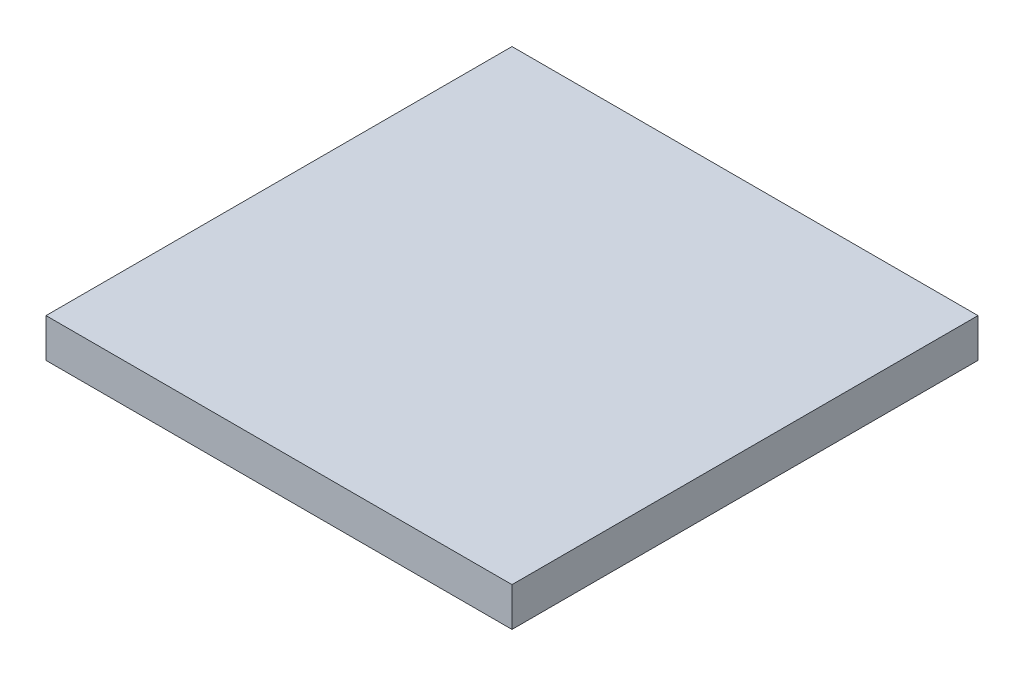
SolidWorks part; units mm, degrees
ref_plane "Front Plane" through (0, 0, 0) normal (0, 0, 1) x (1, 0, 0)
ref_plane "Top Plane" through (0, 0, 0) normal (0, 1, 0) x (1, 0, 0)
ref_plane "Right Plane" through (0, 0, 0) normal (1, 0, 0) x (0, 0, -1)
sketch "BaseS" plane through (0, 0, 0) normal (0, 1, 0) x (1, 0, 0)
  line L1 (-0.6, 0.6) -> (0.6, 0.6)
  line L2 (-0.6, 0.6) -> (-0.6, -0.6)
  line L3 (-0.6, -0.6) -> (0.6, -0.6)
  line L4 (0.6, 0.6) -> (0.6, -0.6)
  line L5 (-0.6, 0.6) -> (0.6, -0.6) construction
  line L6 (-0.6, -0.6) -> (0.6, 0.6) construction
  point P0 (0, 0)
  dimension "Width" = 1.2
  dimension "Length" = 1.2
extrude "Base" add sketch "BaseS" along normal blind 0.1
